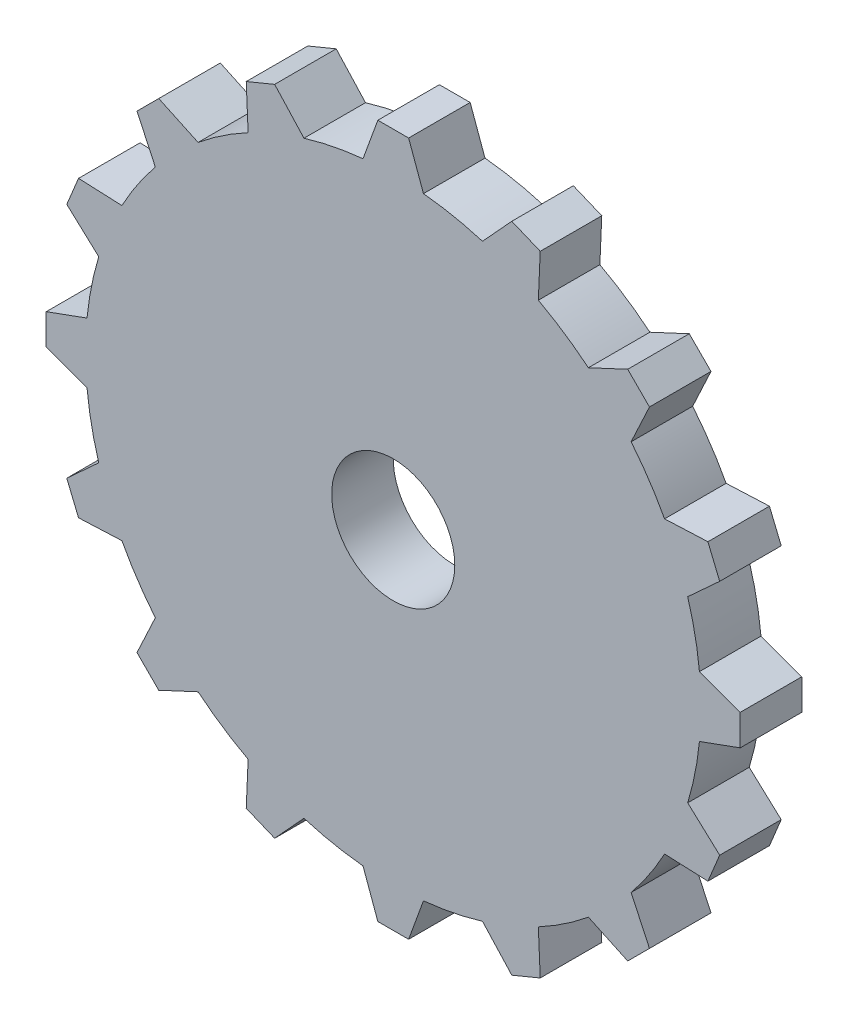
SolidWorks part; units mm, degrees
ref_plane "Front Plane" through (0, 0, 0) normal (0, 0, 1) x (1, 0, 0)
ref_plane "Top Plane" through (0, 0, 0) normal (0, 1, 0) x (1, 0, 0)
ref_plane "Right Plane" through (0, 0, 0) normal (1, 0, 0) x (0, 0, -1)
sketch "Sketch2" plane through (0, 0, 0) normal (0, 0, 1) x (1, 0, 0)
  line L0 (0, 0) -> (9.1887, 0) construction
  line L1 (0, 0) -> (0, 11.2767) construction
  line L2 (-0.25, 5.6384) -> (0.25, 5.6384)
  line L3 (-0.25, 5.6384) -> (-0.25, 4.9937) construction
  line L4 (0.25, 5.6384) -> (0.25, 4.9937) construction
  line L5 (-0.25, 5.6384) -> (-0.4911, 4.9758)
  line L6 (0.25, 5.6384) -> (0.4911, 4.9758)
  line L7 (1.9267, 5.3048) -> (2.3887, 5.1135)
  line L8 (2.3887, 5.1135) -> (2.3579, 4.4091)
  line L9 (1.9267, 5.3048) -> (1.4504, 4.785)
  line L10 (3.8101, 4.1637) -> (4.1637, 3.8101)
  line L11 (4.1637, 3.8101) -> (3.8657, 3.1711)
  line L12 (3.8101, 4.1637) -> (3.1711, 3.8657)
  line L13 (5.1135, 2.3887) -> (5.3048, 1.9267)
  line L14 (5.3048, 1.9267) -> (4.785, 1.4504)
  line L15 (5.1135, 2.3887) -> (4.4091, 2.3579)
  line L16 (5.6384, 0.25) -> (5.6384, -0.25)
  line L17 (5.6384, -0.25) -> (4.9758, -0.4911)
  line L18 (5.6384, 0.25) -> (4.9758, 0.4911)
  line L19 (5.3048, -1.9267) -> (5.1135, -2.3887)
  line L20 (5.1135, -2.3887) -> (4.4091, -2.3579)
  line L21 (5.3048, -1.9267) -> (4.785, -1.4504)
  line L22 (4.1637, -3.8101) -> (3.8101, -4.1637)
  line L23 (3.8101, -4.1637) -> (3.1711, -3.8657)
  line L24 (4.1637, -3.8101) -> (3.8657, -3.1711)
  line L25 (2.3887, -5.1135) -> (1.9267, -5.3048)
  line L26 (1.9267, -5.3048) -> (1.4504, -4.785)
  line L27 (2.3887, -5.1135) -> (2.3579, -4.4091)
  line L28 (0.25, -5.6384) -> (-0.25, -5.6384)
  line L29 (-0.25, -5.6384) -> (-0.4911, -4.9758)
  line L30 (0.25, -5.6384) -> (0.4911, -4.9758)
  line L31 (-1.9267, -5.3048) -> (-2.3887, -5.1135)
  line L32 (-2.3887, -5.1135) -> (-2.3579, -4.4091)
  line L33 (-1.9267, -5.3048) -> (-1.4504, -4.785)
  line L34 (-3.8101, -4.1637) -> (-4.1637, -3.8101)
  line L35 (-4.1637, -3.8101) -> (-3.8657, -3.1711)
  line L36 (-3.8101, -4.1637) -> (-3.1711, -3.8657)
  line L37 (-5.1135, -2.3887) -> (-5.3048, -1.9267)
  line L38 (-5.3048, -1.9267) -> (-4.785, -1.4504)
  line L39 (-5.1135, -2.3887) -> (-4.4091, -2.3579)
  line L40 (-5.6384, -0.25) -> (-5.6384, 0.25)
  line L41 (-5.6384, 0.25) -> (-4.9758, 0.4911)
  line L42 (-5.6384, -0.25) -> (-4.9758, -0.4911)
  line L43 (-5.3048, 1.9267) -> (-5.1135, 2.3887)
  line L44 (-5.1135, 2.3887) -> (-4.4091, 2.3579)
  line L45 (-5.3048, 1.9267) -> (-4.785, 1.4504)
  line L46 (-4.1637, 3.8101) -> (-3.8101, 4.1637)
  line L47 (-3.8101, 4.1637) -> (-3.1711, 3.8657)
  line L48 (-4.1637, 3.8101) -> (-3.8657, 3.1711)
  line L49 (-2.3887, 5.1135) -> (-1.9267, 5.3048)
  line L50 (-1.9267, 5.3048) -> (-1.4504, 4.785)
  line L51 (-2.3887, 5.1135) -> (-2.3579, 4.4091)
  circle A0 centre (0, 0) radius 1
  arc A1 (-2.3579, 4.4091) -> (-3.1711, 3.8657) centre (0, 0) ccw
  arc A2 (-0.4911, 4.9758) -> (-1.4504, 4.785) centre (0, 0) ccw
  arc A3 (1.4504, 4.785) -> (0.4911, 4.9758) centre (0, 0) ccw
  arc A4 (3.1711, 3.8657) -> (2.3579, 4.4091) centre (0, 0) ccw
  arc A5 (4.4091, 2.3579) -> (3.8657, 3.1711) centre (0, 0) ccw
  arc A6 (2.3579, -4.4091) -> (3.1711, -3.8657) centre (0, 0) ccw
  arc A7 (3.8657, -3.1711) -> (4.4091, -2.3579) centre (0, 0) ccw
  arc A8 (4.785, -1.4504) -> (4.9758, -0.4911) centre (0, 0) ccw
  arc A9 (4.9758, 0.4911) -> (4.785, 1.4504) centre (0, 0) ccw
  arc A10 (-3.8657, 3.1711) -> (-4.4091, 2.3579) centre (0, 0) ccw
  arc A11 (-4.785, 1.4504) -> (-4.9758, 0.4911) centre (0, 0) ccw
  arc A12 (-4.9758, -0.4911) -> (-4.785, -1.4504) centre (0, 0) ccw
  arc A13 (-4.4091, -2.3579) -> (-3.8657, -3.1711) centre (0, 0) ccw
  arc A14 (-3.1711, -3.8657) -> (-2.3579, -4.4091) centre (0, 0) ccw
  arc A15 (-1.4504, -4.785) -> (-0.4911, -4.9758) centre (0, 0) ccw
  arc A16 (0.4911, -4.9758) -> (1.4504, -4.785) centre (0, 0) ccw
  point P9 (0, 5.6384)
  point P75 (0, 0)
  dimension "D1" = 2
  dimension "D2" = 10
  dimension "D3" = 0.5
  dimension "D4" = 20
  dimension "D5" = 20
  dimension "D6" = 16
extrude "Boss-Extrude2" add sketch "Sketch2" along normal blind 1
